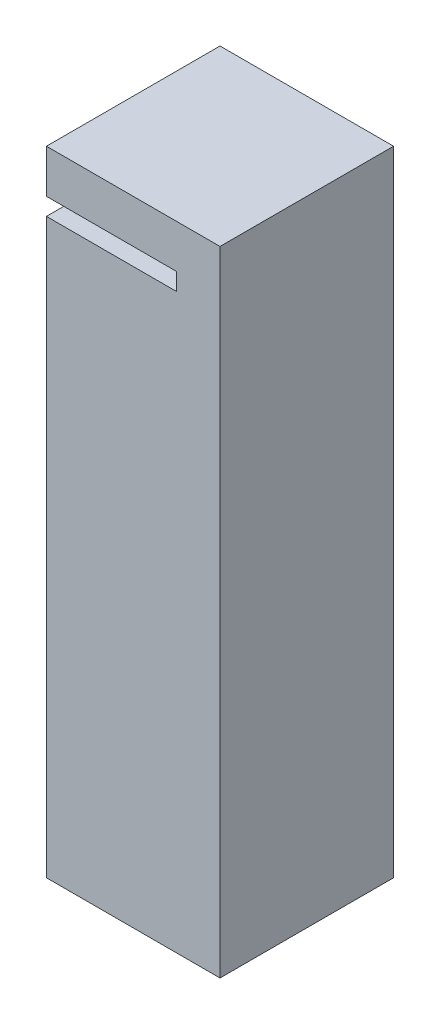
SolidWorks part; units mm, degrees
ref_plane "Plano frontal" through (0, 0, 0) normal (0, 0, 1) x (1, 0, 0)
ref_plane "Plano superior" through (0, 0, 0) normal (0, 1, 0) x (1, 0, 0)
ref_plane "Plano direito" through (0, 0, 0) normal (1, 0, 0) x (0, 0, -1)
sketch "Esboço1" plane through (0, 0, 0) normal (0, 1, 0) x (1, 0, 0)
  line L1 (0, 0) -> (40, 0)
  line L2 (0, 0) -> (0, -40)
  line L3 (0, -40) -> (40, -40)
  line L4 (40, 0) -> (40, -40)
  dimension "D1" = 40
  dimension "D2" = 40
extrude "Ressalto-extrusão1" add sketch "Esboço1" along normal blind 10
sketch "Esboço2" plane through (0, 10, 0) normal (0, 1, 0) x (1, 0, 0)
  line L0 (40, 0) -> (30, 0)
  line L1 (40, 0) -> (0, 0) construction
  line L2 (30, 0) -> (30, -30)
  line L3 (30, -30) -> (0, -30)
  line L4 (0, 0) -> (0, -40) construction
  line L5 (0, -30) -> (0, -40)
  line L6 (0, -40) -> (40, -40)
  line L7 (40, -40) -> (40, 0)
  dimension "D1" = 10
  dimension "D2" = 10
extrude "Ressalto-extrusão2" add sketch "Esboço2" along normal blind 136
sketch "Esboço3" plane through (0, 0, 30) normal (0, 0, -1) x (-1, 0, 0)
  line L0 (-30, 146) -> (-30, 136)
  line L1 (-30, 146) -> (-30, 10) construction
  line L2 (-30, 136) -> (0, 136)
  line L3 (0, 146) -> (0, 10) construction
  line L4 (0, 136) -> (0, 146)
  line L5 (-30, 146) -> (0, 146) construction
  line L6 (0, 146) -> (-30, 146)
  line L7 (-30, 132) -> (0, 132)
  line L8 (-30, 146) -> (-30, 10) construction
  line L9 (0, 132) -> (0, 122)
  line L10 (0, 122) -> (-30, 122)
  line L11 (-30, 122) -> (-30, 132)
  dimension "D1" = 10
  dimension "D2" = 10
  dimension "D3" = 4
extrude "Ressalto-extrusão3" add sketch "Esboço3" along normal up to surface (30 mm away) up to face at (23.3333, 52, 0)
sketch "Esboço4" plane through (0, 0, 30) normal (0, 0, -1) x (-1, 0, 0)
  line L1 (-30, 136) -> (0, 136)
  line L2 (-30, 136) -> (-30, 132)
  line L3 (-30, 132) -> (0, 132)
  line L4 (0, 136) -> (0, 132)
extrude "Corte-extrusão1" cut sketch "Esboço4" against normal through all
